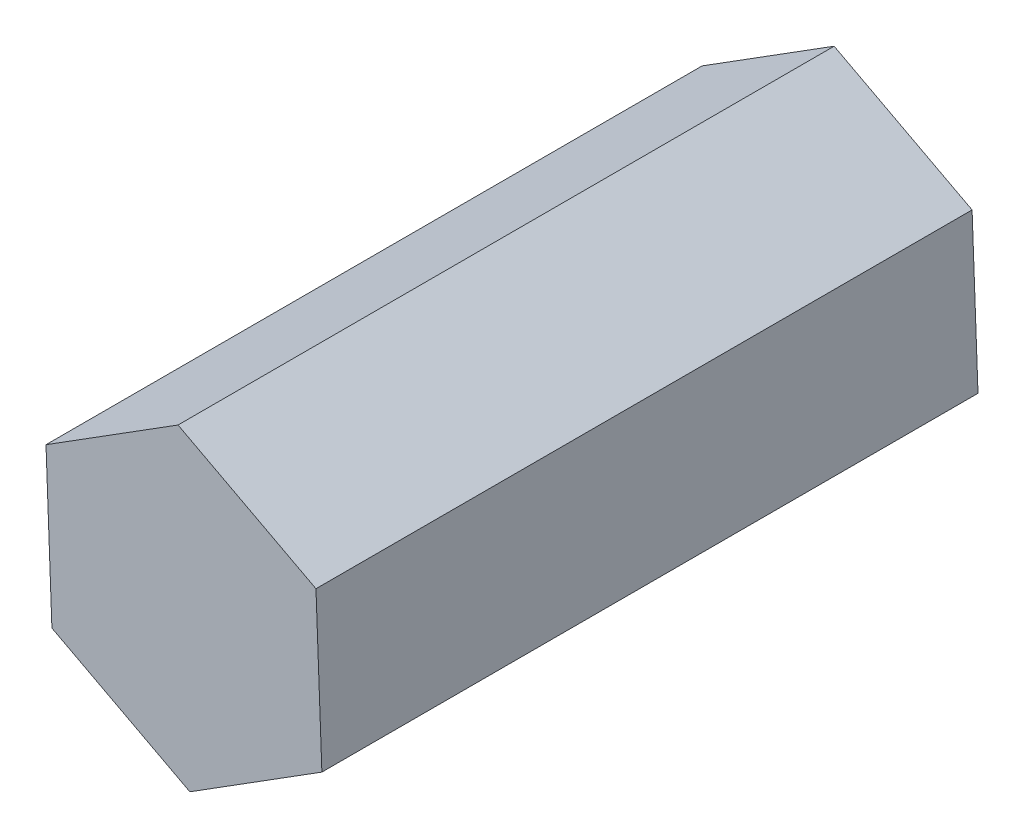
SolidWorks part; units mm, degrees
ref_plane "Front Plane" through (0, 0, 0) normal (0, 0, 1) x (1, 0, 0)
ref_plane "Top Plane" through (0, 0, 0) normal (0, 1, 0) x (1, 0, 0)
ref_plane "Right Plane" through (0, 0, 0) normal (1, 0, 0) x (0, 0, -1)
sketch "Sketch1" plane through (0, 0, 0) normal (0, 0, 1) x (1, 0, 0)
  line L1 (3.5742, -1.8864) -> (3.4208, 2.1522)
  line L2 (3.4208, 2.1522) -> (-0.1534, 4.0385)
  line L3 (-0.1534, 4.0385) -> (-3.5742, 1.8864)
  line L4 (-3.5742, 1.8864) -> (-3.4208, -2.1522)
  line L5 (-3.4208, -2.1522) -> (0.1534, -4.0385)
  line L6 (0.1534, -4.0385) -> (3.5742, -1.8864)
  circle A0 centre (0, 0) radius 3.5 construction
  point P1 (3.4975, 0.1329)
  dimension "D1" = 7
extrude "Boss-Extrude1" add sketch "Sketch1" along normal blind 17
sketch "Sketch2" plane through (0, 0, 0) normal (0, 0, 1) x (1, 0, 0)
  line L0 (0.76, 1.2932) -> (1.1954, -0.9062)
  arc A0 (0.76, 1.2932) -> (1.1954, -0.9062) centre (0, 0) ccw
ref_plane "Plane4" through (0, 0, 17) normal (0, 0, 1) x (1, 0, 0)
extrude "Cut-Extrude7" cut sketch "Sketch2" along normal blind 8
